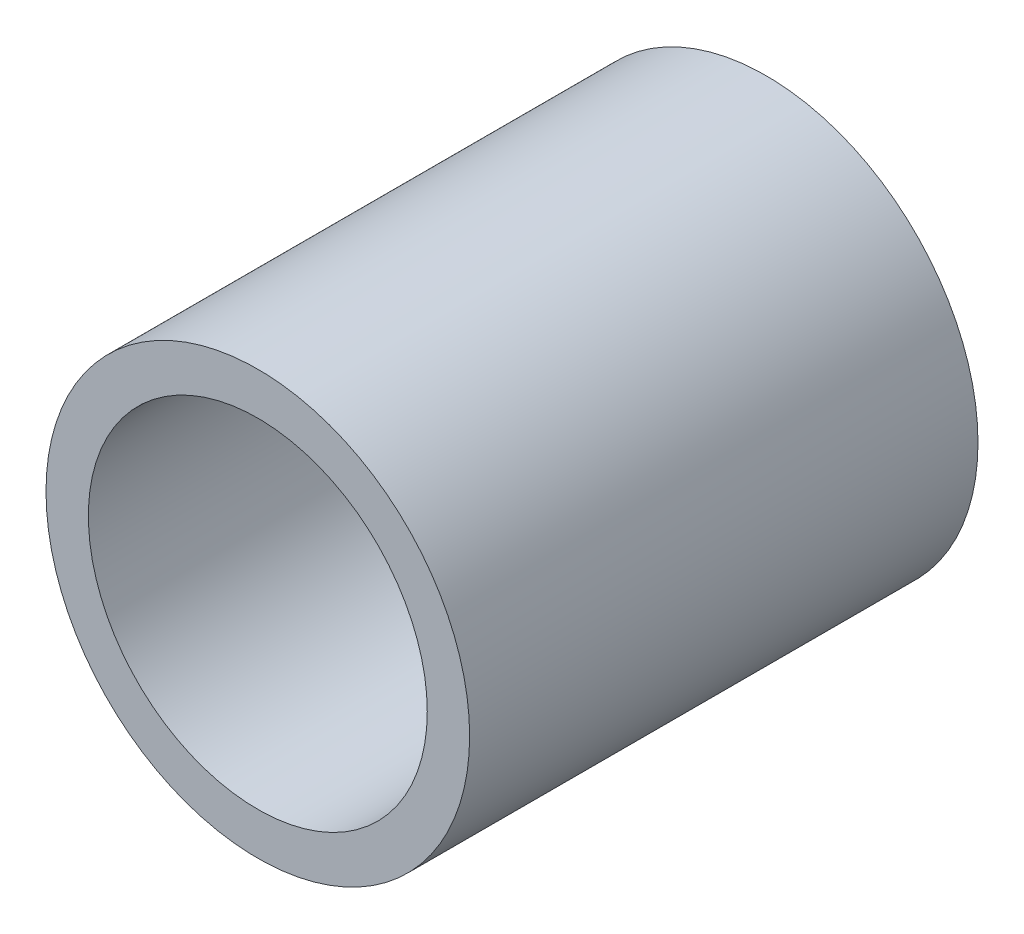
SolidWorks part; units mm, degrees
ref_plane "前视基准面" through (0, 0, 0) normal (0, 0, 1) x (1, 0, 0)
ref_plane "上视基准面" through (0, 0, 0) normal (0, 1, 0) x (1, 0, 0)
ref_plane "右视基准面" through (0, 0, 0) normal (1, 0, 0) x (0, 0, -1)
sketch "草图1" plane through (0, 0, 0) normal (0, 0, 1) x (1, 0, 0)
  circle A1 centre (0, 0) radius 2.5
  dimension "D2" = 5
extrude "凸台-拉伸1" add sketch "草图1" along normal blind 6
shell "抽壳1" thickness 0.5
